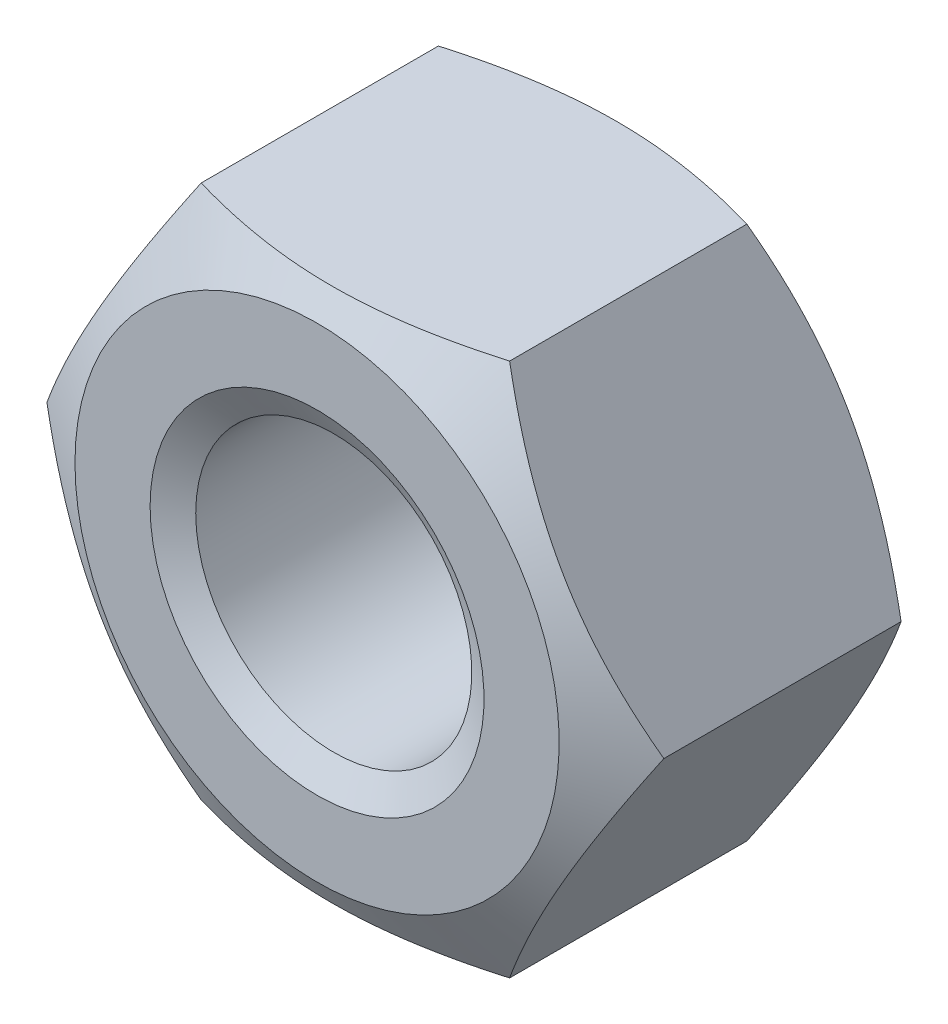
SolidWorks part; units mm, degrees
ref_plane "Front" through (0, 0, 0) normal (0, 0, 1) x (1, 0, 0)
ref_plane "Top" through (0, 0, 0) normal (0, 1, 0) x (1, 0, 0)
ref_plane "Right" through (0, 0, 0) normal (1, 0, 0) x (0, 0, -1)
sketch "Sketch1" plane through (0, 0, 0) normal (0, 0, 1) x (1, 0, 0)
  line L1 (4.6188, 0) -> (2.3094, 4)
  line L2 (2.3094, 4) -> (-2.3094, 4)
  line L3 (-2.3094, 4) -> (-4.6188, 0)
  line L4 (-4.6188, 0) -> (-2.3094, -4)
  line L5 (-2.3094, -4) -> (2.3094, -4)
  line L6 (2.3094, -4) -> (4.6188, 0)
  circle A0 centre (0, 0) radius 4 construction
  circle A1 centre (0, 0) radius 2.067
  dimension "D" = 4.134
  dimension "s" = 8
extrude "BaseNut" add sketch "Sketch1" against normal blind 4.7
cosmetic thread "ThreadCosmetic1" parameters "D"=5
sketch "Sketch2" plane through (0, 0, 0) normal (0, 1, 0) x (1, 0, 0)
  line L0 (-4.6188, 4.7) -> (-3.625, 4.7)
  line L2 (-3.625, 4.7) -> (-4.6188, 4.1262)
  line L3 (-4.6188, 4.1262) -> (-4.6188, 4.7)
  line L4 (0, 3.3759) -> (0, -9.8171) construction
  line L6 (-9.7712, 2.35) -> (9.8853, 2.35) construction
  line L7 (-4.6188, 0.5738) -> (-4.6188, 0)
  line L8 (-3.625, 0) -> (-4.6188, 0.5738)
  line L9 (-4.6188, 0) -> (-3.625, 0)
  dimension "dw" = 7.25
  dimension "D1" = 30
  dimension "D2" = 2.35
revolve "Double-Chamfer" cut sketch "Sketch2" angle 360 about L4
chamfer "EndChamfer" distance 0.433 angle 30 2 edges at (2.067, 0, -4.7) (2.067, 0, 0)
sketch "Sketch3" plane through (0, 0, 0) normal (0, 1, 0) x (1, 0, 0)
  line L0 (-2.442, 4.267) -> (-2.067, 4.0505)
  line L1 (-2.067, 4.0505) -> (-1.634, 4.0505)
  line L2 (-1.634, 4.0505) -> (-1.634, 4.4835)
  line L3 (-1.634, 4.4835) -> (-2.067, 4.4835)
  line L4 (-2.067, 4.4835) -> (-2.442, 4.267)
  line L5 (0, 7.4383) -> (0, 16.8806) construction
  dimension "D1" = 0.433
  dimension "D2" = 4.134
revolve "Cut-Revolve10" [suppressed] cut sketch "Sketch3" angle 360 about L5
pattern_linear "LPattern10" [suppressed] count 9 spacing 0.5196 along (0, 0, -1)
equation "\"dw@Sketch2\" = \"s@Sketch1\"-0.75"
equation "\"D2@Sketch2\" = \"m@BaseNut\" / 2"
equation "\"D2@Sketch3\" = \"D@Sketch1\""
equation "\"D1@Sketch3\" =  (\"D@ThreadCosmetic1\"   - \"D@Sketch1\")  / 2"
equation "\"D3@LPattern10\" = \"D1@Sketch3\" * 1.2"
equation "\"D1@LPattern10\" = \"m@BaseNut\"/\"D3@LPattern10\""
